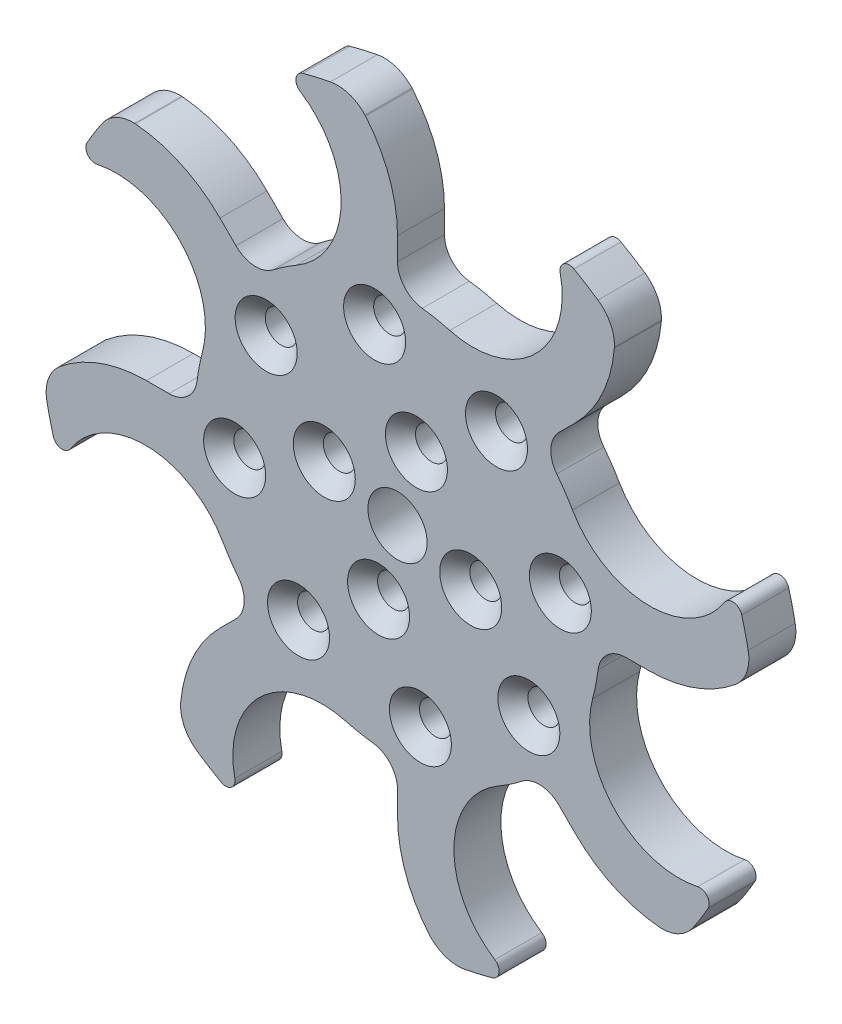
SolidWorks part; units mm, degrees
material "Thornel Mat VMA"
ref_plane "前视基准面" through (0, 0, 0) normal (0, 0, 1) x (1, 0, 0)
ref_plane "上视基准面" through (0, 0, 0) normal (0, 1, 0) x (1, 0, 0)
ref_plane "右视基准面" through (0, 0, 0) normal (1, 0, 0) x (0, 0, -1)
sketch "草图1" plane through (0, 0, 0) normal (0, 0, 1) x (1, 0, 0)
  line L0 (0, 0) -> (50000, 0) construction
  line L1 (0, 0) -> (0, -50000) construction
  line L2 (0, 0) -> (-10.75, 18.6195) construction
  line L3 (0, 21.5) -> (0, 26.7215)
  line L4 (-3.4, 36.0376) -> (32202.7815, -38210.0324) construction
  circle A0 centre (0, 0) radius 21.5
  arc A1 (0, 26.7215) -> (-3.4, 36.0376) centre (-14.4632, 26.7215) ccw
  arc A2 (-3.4, 36.0376) -> (-3.4606, 36.1064) centre (-4.9298, 34.7494) ccw
  arc A3 (-3.4606, 36.1064) -> (-7.1519, 37.3209) centre (-6.3991, 33.3924) ccw
  circle A4 centre (0, 0) radius 38 construction
  arc A5 (-7.1519, 37.3209) -> (-10.0801, 36.6387) centre (0, 0) ccw
  arc A6 (-10.0801, 36.6387) -> (-10.7994, 35.4998) centre (-9.8148, 35.6745) ccw
  arc A7 (-10.7994, 35.4998) -> (-10.3562, 34.8338) centre (-9.8148, 35.6745) ccw
  arc A8 (-10.3562, 34.8338) -> (-10.75, 18.6195) centre (-15.5, 26.8468) cw
  point P29 (0, 32)
  dimension "D1" = 43
  dimension "D3" = 76
  dimension "D5" = 2
  dimension "D6" = 4
  dimension "D7" = 40.1
  dimension "D8" = 1
  dimension "D9" = 1
  dimension "D11" = 9.5
  dimension "D2" = 30
  dimension "D4" = 3.4
  dimension "D10" = 0.8
  dimension "D12" = 32
extrude "凸台-拉伸1" add sketch "草图1" along normal blind 5 contours A7 A8 A0 L3 A1 A2 A3 A5 A6 | A0 A5
pattern_circular "阵列(圆周)1" count 8 over 360 about axis through (0, 0, 0) along (0, 0, 1) of "凸台-拉伸1"
fillet "圆角1" radius 3 8 edges at (15.2028, 15.2028, 2.5) (21.5, 0, 2.5) (15.2028, -15.2028, 2.5) (0, -21.5, 2.5) (-15.2028, -15.2028, 2.5) (-21.5, 0, 2.5) (-15.2028, 15.2028, 2.5) (0, 21.5, 2.5)
sketch "草图4" plane through (0, 0, 5) normal (0, 0, 1) x (1, 0, 0)
  line L0 (0, 0) -> (50000, 0) construction
  line L1 (0, 0) -> (0, -50000) construction
  line L2 (-2.4355, 17.3297) -> (0, 0) construction
  line L3 (10.5318, 13.9761) -> (0, 0) construction
  line L4 (2.0156, 7.7936) -> (0, 0) construction
  circle A0 centre (0, 0) radius 17.5 construction
  circle A1 centre (-2.4355, 17.3297) radius 1.6
  circle A7 centre (0, 0) radius 8.05 construction
  circle A8 centre (10.5318, 13.9761) radius 1.6
  circle A9 centre (17.3297, 2.4355) radius 1.6
  circle A10 centre (13.9761, -10.5318) radius 1.6
  circle A11 centre (2.4355, -17.3297) radius 1.6
  circle A12 centre (-10.5318, -13.9761) radius 1.6
  circle A13 centre (-17.3297, -2.4355) radius 1.6
  circle A14 centre (-13.9761, 10.5318) radius 1.6
  circle A15 centre (2.0156, 7.7936) radius 1.65
  circle A16 centre (7.7936, -2.0156) radius 1.65
  circle A17 centre (-2.0156, -7.7936) radius 1.65
  circle A18 centre (-7.7936, 2.0156) radius 1.65
  circle A19 centre (0, 0) radius 3.15
  point P22 (0, 0)
  point P28 (0, 0)
  point P37 (0, 0)
  dimension "D1" = 35
  dimension "D2" = 3.2
  dimension "D5" = 16.1
  dimension "D6" = 3.3
  dimension "D9" = 6.3
  dimension "D3" = 8
  dimension "D7" = 22.5
  dimension "D8" = 4
  dimension "D4" = 8
extrude "切除-拉伸2" cut sketch "草图4" against normal blind 5
hole_wizard "打孔尺寸(%根据十字)槽半沉头木螺钉的类型1" positions "3D草图1" profile "草图5" countersink size "M3" standard "GB" end condition through all
sketch3d "3D草图1"
  line L0 (-13.9761, 10.5318, 0) -> (-13.9761, 10.5318, 5) construction
  line L1 (-2.4355, 17.3297, 0) -> (-2.4355, 17.3297, 5) construction
  line L2 (10.5318, 13.9761, 0) -> (10.5318, 13.9761, 5) construction
  line L3 (17.3297, 2.4355, 0) -> (17.3297, 2.4355, 5) construction
  line L4 (13.9761, -10.5318, 0) -> (13.9761, -10.5318, 5) construction
  line L5 (2.4355, -17.3297, 0) -> (2.4355, -17.3297, 5) construction
  line L6 (-10.5318, -13.9761, 0) -> (-10.5318, -13.9761, 5) construction
  line L7 (-17.3297, -2.4355, 0) -> (-17.3297, -2.4355, 5) construction
  line L8 (-7.7936, 2.0156, 0) -> (-7.7936, 2.0156, 5) construction
  line L9 (2.0156, 7.7936, 0) -> (2.0156, 7.7936, 5) construction
  line L10 (7.7936, -2.0156, 0) -> (7.7936, -2.0156, 5) construction
  line L11 (-2.0156, -7.7936, 0) -> (-2.0156, -7.7936, 5) construction
  point P0 (-13.9761, 10.5318, 5)
  point P4 (-2.4355, 17.3297, 5)
  point P8 (10.5318, 13.9761, 5)
  point P12 (17.3297, 2.4355, 5)
  point P16 (13.9761, -10.5318, 5)
  point P20 (2.4355, -17.3297, 5)
  point P24 (-10.5318, -13.9761, 5)
  point P28 (-17.3297, -2.4355, 5)
  point P32 (-7.7936, 2.0156, 5)
  point P36 (2.0156, 7.7936, 5)
  point P40 (7.7936, -2.0156, 5)
  point P44 (-2.0156, -7.7936, 5)
sketch "草图5" plane through (-13.9761, 10.5318, 5) normal (1, 0, 0) x (0, -1, 0)
  line L0 (0, 0) -> (0, 5)
  line L1 (0, 5) -> (1.7, 5)
  line L2 (1.7, 5) -> (1.7, 1.6)
  line L3 (1.7, 1.6) -> (3.3, 0)
  line L5 (3.3, 0) -> (0, 0)
  line L6 (-1.7, 1.6) -> (-3.3, 0) construction
  line L11 (0, -6.35) -> (0, 107.95) construction
  dimension "通孔孔直径" = 3.4
  dimension "通孔孔深度" = 5
  dimension "近端锥形沉头孔直径" = 6.6
  dimension "近端锥形沉头孔角度" = 90
